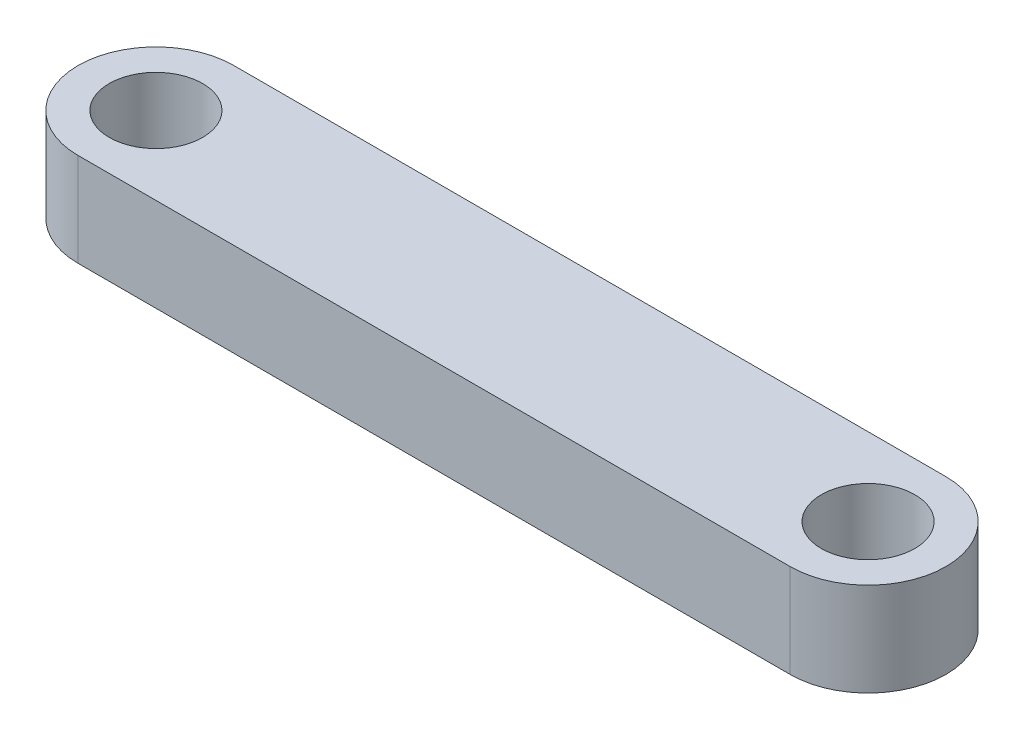
SolidWorks part; units mm, degrees
ref_plane "Front Plane" through (0, 0, 0) normal (0, 0, 1) x (1, 0, 0)
ref_plane "Top Plane" through (0, 0, 0) normal (0, 1, 0) x (1, 0, 0)
ref_plane "Right Plane" through (0, 0, 0) normal (1, 0, 0) x (0, 0, -1)
sketch "Sketch1" plane through (0, 0, 0) normal (0, 1, 0) x (1, 0, 0)
  line L0 (-11.43, 0) -> (11.43, 0) construction
  line L1 (-13.93, 2.5) -> (-11.43, 2.5) construction
  line L2 (-11.43, 2.5) -> (11.43, 2.5)
  line L3 (-13.93, 2.5) -> (-13.93, -2.5) construction
  line L4 (-11.43, -2.5) -> (11.43, -2.5)
  line L5 (13.93, 2.5) -> (13.93, -2.5) construction
  line L6 (-12.5244, 2.2477) -> (12.5244, -2.2477) construction
  line L7 (-12.5244, -2.2477) -> (12.5244, 2.2477) construction
  line L8 (-13.93, 2.5) -> (-12.5244, 2.2477) construction
  line L9 (-13.93, -2.5) -> (-12.5244, -2.2477) construction
  line L10 (-13.93, -2.5) -> (-11.43, -2.5) construction
  line L11 (11.43, 2.5) -> (13.93, 2.5) construction
  line L12 (12.5244, 2.2477) -> (13.93, 2.5) construction
  line L13 (11.43, -2.5) -> (13.93, -2.5) construction
  line L14 (12.5244, -2.2477) -> (13.93, -2.5) construction
  circle A0 centre (-11.43, 0) radius 1.5
  circle A1 centre (11.43, 0) radius 1.5
  arc A2 (-11.43, 2.5) -> (-11.43, -2.5) centre (-11.43, 0) ccw
  arc A3 (11.43, -2.5) -> (11.43, 2.5) centre (11.43, 0) ccw
  point P4 (0, 0)
  point P10 (0, 0)
  dimension "D1" = 3
  dimension "D2" = 22.86
  dimension "D4" = 5
  dimension "D3" = 22.86
extrude "Boss-Extrude2" add sketch "Sketch1" along normal mid plane 3
